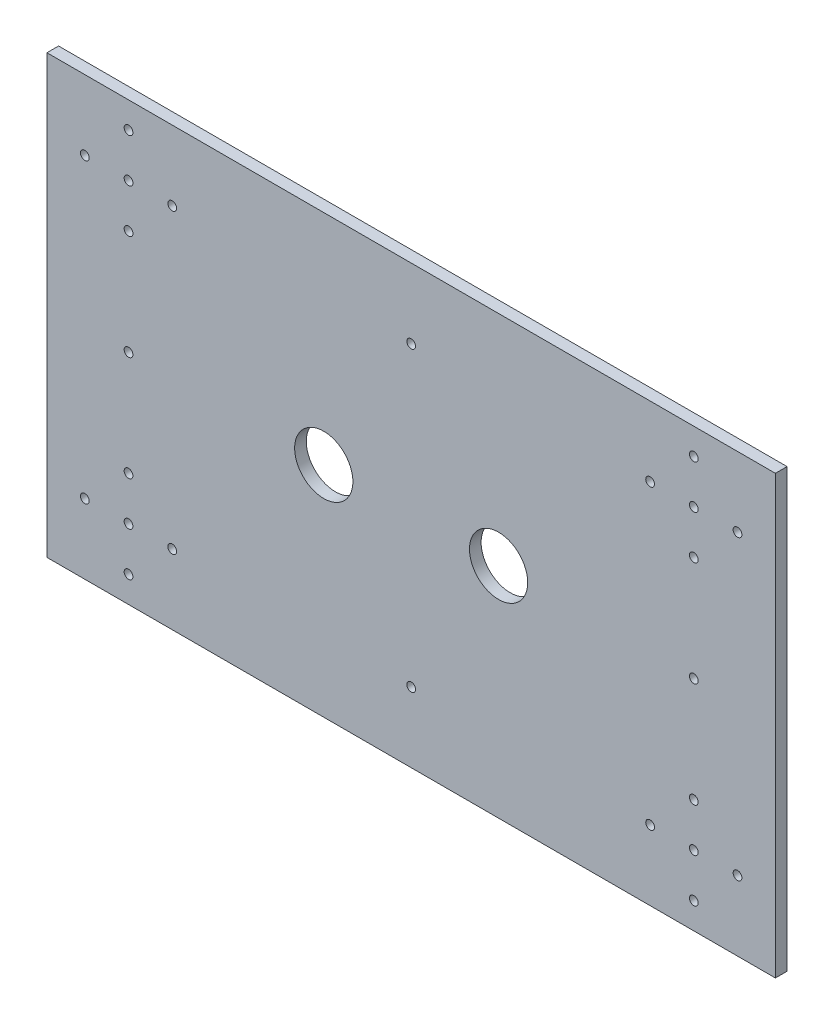
SolidWorks part; units mm, degrees
ref_plane "Front Plane" through (0, 0, 0) normal (0, 0, 1) x (1, 0, 0)
ref_plane "Top Plane" through (0, 0, 0) normal (0, 1, 0) x (1, 0, 0)
ref_plane "Right Plane" through (0, 0, 0) normal (1, 0, 0) x (0, 0, -1)
sketch "Sketch1" plane through (0, 0, 0) normal (0, 0, 1) x (1, 0, 0)
  line L1 (-60.0985, 33.8667) -> (189.9015, 33.8667)
  line L2 (-60.0985, 33.8667) -> (-60.0985, -116.1333)
  line L3 (-60.0985, -116.1333) -> (189.9015, -116.1333)
  line L4 (189.9015, 33.8667) -> (189.9015, -116.1333)
  circle A0 centre (-32.0985, -92.1333) radius 1.5
  circle A1 centre (-17.0985, -92.1333) radius 1.5
  circle A2 centre (-32.0985, -107.1333) radius 1.5
  circle A3 centre (-47.0985, -92.1333) radius 1.5
  circle A4 centre (-32.0985, -77.1333) radius 1.5
  circle A5 centre (176.9015, -92.1333) radius 1.5
  circle A6 centre (161.9015, -92.1333) radius 1.5
  circle A7 centre (161.9015, -77.1333) radius 1.5
  circle A8 centre (146.9015, -92.1333) radius 1.5
  circle A9 centre (161.9015, -107.1333) radius 1.5
  circle A10 centre (176.9015, 9.8667) radius 1.5
  circle A11 centre (161.9015, 9.8667) radius 1.5
  circle A12 centre (161.9015, 24.8667) radius 1.5
  circle A13 centre (146.9015, 9.8667) radius 1.5
  circle A14 centre (161.9015, -5.1333) radius 1.5
  circle A15 centre (-17.0985, 9.8667) radius 1.5
  circle A16 centre (-32.0985, 9.8667) radius 1.5
  circle A17 centre (-32.0985, 24.8667) radius 1.5
  circle A18 centre (-47.0985, 9.8667) radius 1.5
  circle A19 centre (-32.0985, -5.1333) radius 1.5
  circle A20 centre (-32.0985, -41.1333) radius 1.5
  circle A21 centre (161.9015, -41.1333) radius 1.5
  circle A22 centre (64.9015, 9.8667) radius 1.5
  circle A23 centre (64.9015, -92.1333) radius 1.5
  circle A24 centre (94.9015, -41.1333) radius 10
  circle A25 centre (34.9015, -41.1333) radius 10
  point P28 (-32.0985, -92.1333)
  dimension "D1" = 2
  dimension "D2" = 2
  dimension "D3" = 24
  dimension "D5" = 15
  dimension "D7" = 2
  dimension "D8" = 2
  dimension "D6" = 4
extrude "Boss-Extrude1" add sketch "Sketch1" along normal blind 4
